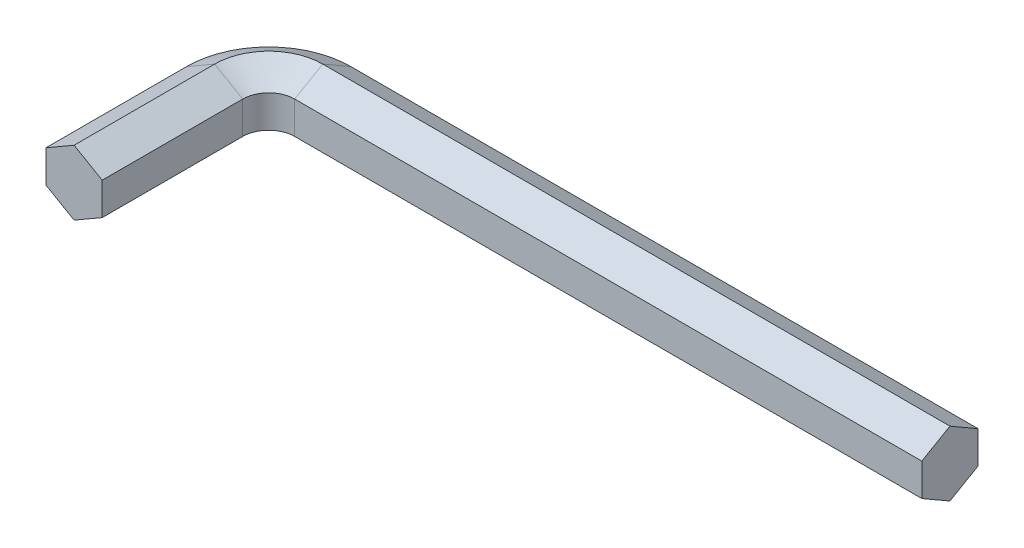
SolidWorks part; units mm, degrees
ref_plane "Front Plane" through (0, 0, 0) normal (0, 0, 1) x (1, 0, 0)
ref_plane "Top Plane" through (0, 0, 0) normal (0, 1, 0) x (1, 0, 0)
ref_plane "Right Plane" through (0, 0, 0) normal (1, 0, 0) x (0, 0, -1)
sketch "Sketch1" plane through (0, 0, 0) normal (0, 1, 0) x (1, 0, 0)
  line L1 (-26.5, 11) -> (31.5, 11)
  line L2 (-31.5, 6) -> (-31.5, -7)
  arc A0 (-31.5, 6) -> (-26.5, 11) centre (-26.5, 6) cw
  point P0 (0, 0)
  point P7 (-31.5, 11)
  dimension "D3" = 5
  dimension "D1" = 63
  dimension "D2" = 18
ref_plane "Plane1" through (31.5, 0, -11) normal (1, 0, 0) x (0, 0, -1)
sketch "Sketch2" plane through (31.5, 0, -11) normal (1, 0, 0) x (0, 0, -1)
  line L1 (-2.5981, 1.5) -> (-2.5981, -1.5)
  line L2 (-2.5981, -1.5) -> (0, -3)
  line L3 (0, -3) -> (2.5981, -1.5)
  line L4 (2.5981, -1.5) -> (2.5981, 1.5)
  line L5 (2.5981, 1.5) -> (0, 3)
  line L6 (0, 3) -> (-2.5981, 1.5)
  circle A0 centre (0, 0) radius 2.5981 construction
  dimension "D1" = 3
sweep "Sweep1" add profiles "Sketch2" path "Sketch1"
